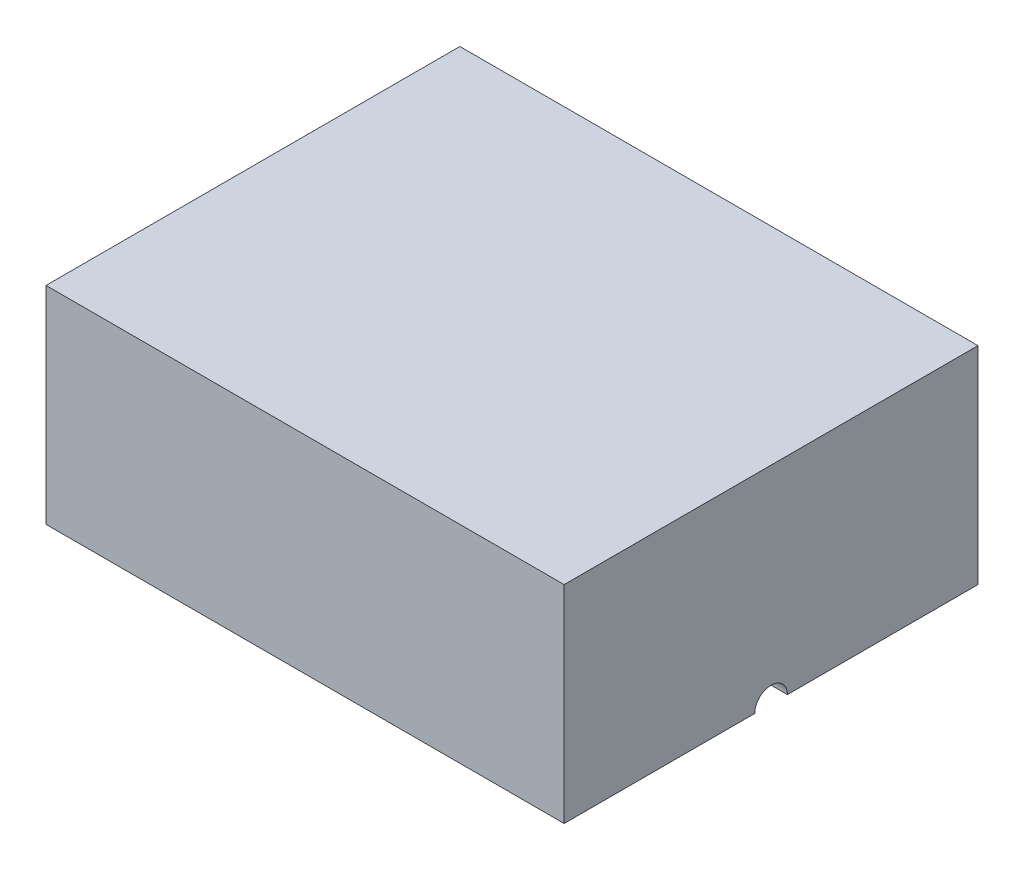
SolidWorks part; units mm, degrees
ref_plane "Front Plane" through (0, 0, 0) normal (0, 0, 1) x (1, 0, 0)
ref_plane "Top Plane" through (0, 0, 0) normal (0, 1, 0) x (1, 0, 0)
ref_plane "Right Plane" through (0, 0, 0) normal (1, 0, 0) x (0, 0, -1)
sketch "Sketch1" plane through (0, 0, 0) normal (0, 1, 0) x (1, 0, 0)
  line L1 (15.9, 12.7) -> (-15.9, 12.7)
  line L2 (15.9, 12.7) -> (15.9, -12.7)
  line L3 (15.9, -12.7) -> (-15.9, -12.7)
  line L4 (-15.9, 12.7) -> (-15.9, -12.7)
  line L5 (15.9, 12.7) -> (-15.9, -12.7) construction
  line L6 (15.9, -12.7) -> (-15.9, 12.7) construction
  point P0 (0, 0)
extrude "Boss-Extrude1" add sketch "Sketch1" along normal blind 12.7
sketch "Sketch2" plane through (0, 0, 0) normal (0, -1, 0) x (1, 0, 0)
  line L1 (0, 0) -> (15.9, 0) construction
  line L2 (15.9, 12.7) -> (15.9, -12.7) construction
  line L5 (-14, 0) -> (14, 0)
  line L6 (0, 0) -> (0, 12.7) construction
  line L7 (-15.9, 12.7) -> (15.9, 12.7) construction
  ellipse E0 centre (0, 0) end of major axis (-14, 0) minor radius 9.38 (0, 9.38) -> (14, 0) cw
  ellipse E2 centre (0, 0) end of major axis (14, 0) minor radius 9.38 (0, 9.38) -> (-14, 0) ccw
revolve "Cut-Revolve8" cut sketch "Sketch2" angle 360 mid plane about L1
sketch "Sketch7" plane through (15.9, 0, 0) normal (1, 0, 0) x (0, 0, -1)
  circle A0 centre (0, 0) radius 1
extrude "Cut-Extrude1" cut sketch "Sketch7" against normal through all
sketch "Sketch8" plane through (0, 0, 0) normal (0, -1, 0) x (-1, 0, 0)
  line L0 (0, 0) -> (-15.9, 0) construction
  line L1 (-15.9, 1) -> (-15.9, -1) construction
  line L2 (0, 0) -> (0, -12.7) construction
  line L3 (15.9, -12.7) -> (-15.9, -12.7) construction
